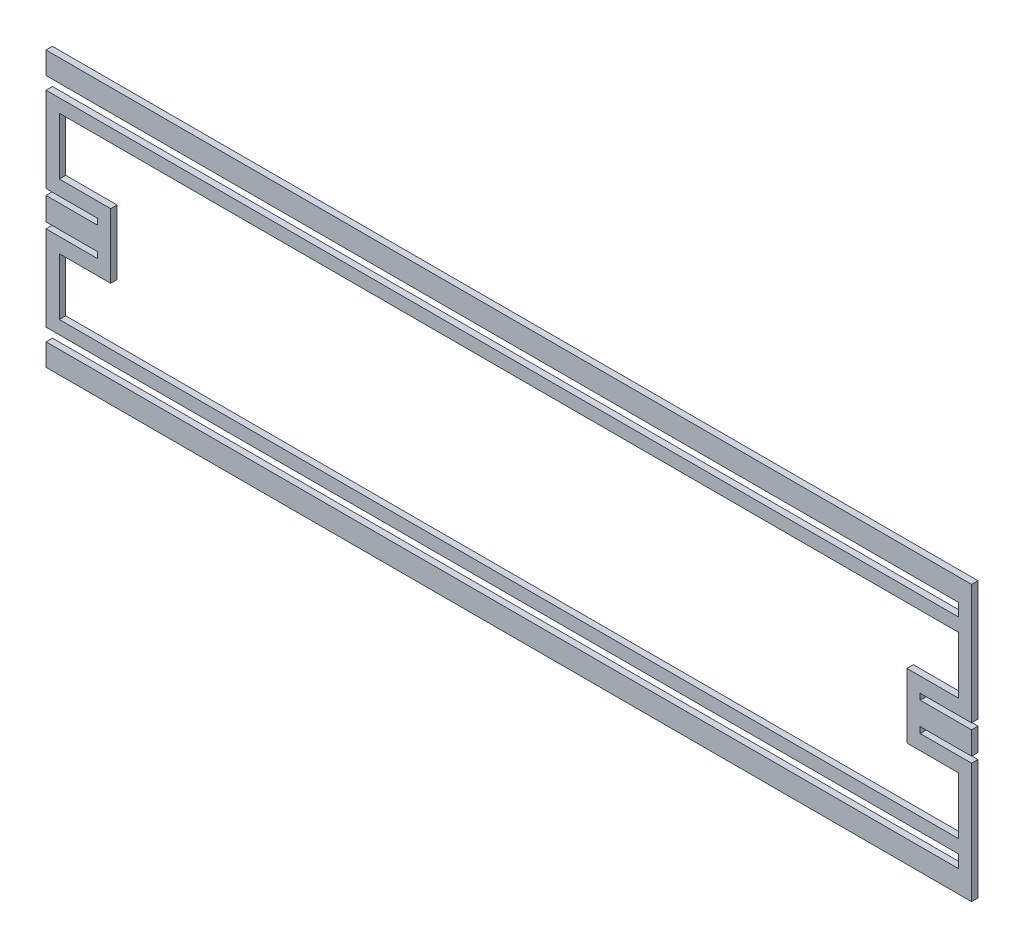
SolidWorks part; units mm, degrees
ref_plane "Front" through (0, 0, 0) normal (0, 0, 1) x (1, 0, 0)
ref_plane "Top" through (0, 0, 0) normal (0, 1, 0) x (1, 0, 0)
ref_plane "Right" through (0, 0, 0) normal (1, 0, 0) x (0, 0, -1)
sketch "Sketch1" plane through (0, 0, 0) normal (0, 0, 1) x (1, 0, 0)
  line L0 (-228.7016, 8.6296) -> (-203.3016, 8.6296)
  line L1 (-203.3016, 8.6296) -> (-203.3016, 5.6579)
  line L2 (-203.3016, 5.6579) -> (-228.7016, 5.6578)
  line L3 (-228.7016, 5.6578) -> (-228.7016, -5.6578)
  line L4 (-228.7016, -5.6578) -> (-203.3016, -5.6579)
  line L5 (-203.3016, -5.6579) -> (-203.3016, -8.6297)
  line L6 (-203.3016, -8.6297) -> (-228.7016, -8.6297)
  line L7 (-228.7016, -8.6297) -> (-228.7016, -50.7047)
  line L8 (-228.7016, -50.7047) -> (222.1484, -50.7047)
  line L9 (222.1484, -50.7047) -> (222.1484, -56.9785)
  line L10 (222.1484, -56.9785) -> (-228.7016, -56.9785)
  line L11 (-228.7016, -56.9785) -> (-228.7016, -67.8974)
  line L12 (-228.7016, -67.8974) -> (228.7016, -67.8974)
  line L13 (228.7016, -67.8974) -> (228.7016, -8.6297)
  line L14 (228.7016, -8.6297) -> (203.3016, -8.6297)
  line L15 (203.3016, -8.6297) -> (203.3016, -5.6579)
  line L16 (203.3016, -5.6579) -> (228.7016, -5.6578)
  line L17 (228.7016, -5.6578) -> (228.7016, 5.6578)
  line L18 (228.7016, 5.6578) -> (203.3016, 5.6579)
  line L19 (203.3016, 5.6579) -> (203.3016, 8.6296)
  line L20 (203.3016, 8.6296) -> (228.7016, 8.6296)
  line L21 (228.7016, 8.6296) -> (228.7016, 67.8974)
  line L22 (228.7016, 67.8974) -> (-228.7016, 67.8974)
  line L23 (-228.7016, 67.8974) -> (-228.7016, 56.9785)
  line L24 (-228.7016, 56.9785) -> (222.1484, 56.9785)
  line L25 (222.1484, 56.9785) -> (222.1484, 50.7047)
  line L26 (222.1484, 50.7047) -> (-228.7016, 50.7047)
  line L27 (-228.7016, 50.7047) -> (-228.7016, 8.6296)
  line L28 (222.1484, -44.1516) -> (222.1484, -15.9766)
  line L29 (222.1484, -15.9766) -> (196.7484, -15.9766)
  line L30 (196.7484, -15.9766) -> (196.7484, 15.9766)
  line L31 (196.7484, 15.9766) -> (222.1484, 15.9766)
  line L32 (222.1484, 15.9766) -> (222.1484, 44.1516)
  line L33 (-222.1484, -44.1516) -> (222.1484, -44.1516)
  line L34 (-222.1484, -15.9766) -> (-222.1484, -44.1516)
  line L35 (-196.7484, -15.9766) -> (-222.1484, -15.9766)
  line L36 (-196.7484, 15.9766) -> (-196.7484, -15.9766)
  line L37 (-222.1484, 15.9766) -> (-196.7484, 15.9766)
  line L38 (-222.1484, 44.1516) -> (-222.1484, 15.9766)
  line L39 (222.1484, 44.1516) -> (-222.1484, 44.1516)
extrude "Boss-Extrude1" add sketch "Sketch1" along normal blind 3.175
